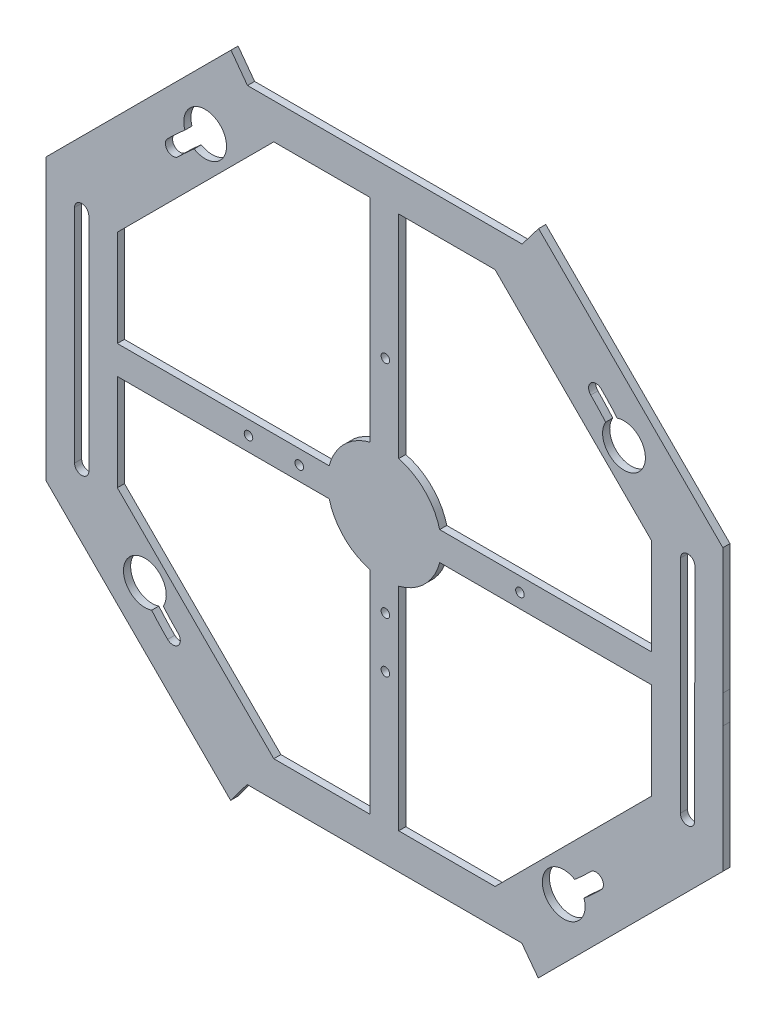
SolidWorks part; units mm, degrees
material "6061-T6 (SS)"
ref_plane "Front Plane" through (0, 0, 0) normal (0, 0, 1) x (1, 0, 0)
ref_plane "Top Plane" through (0, 0, 0) normal (0, 1, 0) x (1, 0, 0)
ref_plane "Right Plane" through (0, 0, 0) normal (1, 0, 0) x (0, 0, -1)
sketch "Sketch1" plane through (0, 0, 0) normal (0, 0, 1) x (1, 0, 0)
  line L0 (-150.6696, -62.417) -> (-62.404, -150.675)
  line L1 (-137.9698, -57.1559) -> (-57.1441, -137.9748)
  line L2 (-57.1441, -137.9748) -> (57.1559, -137.9698)
  line L3 (57.1559, -137.9698) -> (137.9748, -57.1441)
  line L4 (137.9748, -57.1441) -> (137.9698, 57.1559)
  line L5 (137.9698, 57.1559) -> (57.1441, 137.9748)
  line L6 (57.1441, 137.9748) -> (-57.1559, 137.9698)
  line L7 (-57.1559, 137.9698) -> (-137.9748, 57.1441)
  line L8 (-137.9748, 57.1441) -> (-137.9698, -57.1559)
  line L9 (-62.404, -150.675) -> (62.417, -150.6696)
  line L10 (62.417, -150.6696) -> (150.675, -62.404)
  line L11 (150.675, -62.404) -> (150.6696, 62.417)
  line L12 (150.6696, 62.417) -> (62.404, 150.675)
  line L13 (62.404, 150.675) -> (-62.417, 150.6696)
  line L14 (-62.417, 150.6696) -> (-150.675, 62.404)
  line L15 (-150.675, 62.404) -> (-150.6696, -62.417)
  circle A0 centre (0, 0) radius 137.9723 construction
  circle A1 centre (0, 0) radius 150.6723 construction
  dimension "D2" = 12.7
  dimension "D1" = 114.3
extrude "Boss-Extrude1" add sketch "Sketch1" along normal blind 3.175
sketch "Sketch2" plane through (0, 0, 3.175) normal (0, 0, 1) x (1, 0, 0)
  line L0 (57.1441, 137.9748) -> (-57.1559, 137.9698) construction
  line L1 (-57.1559, 137.9698) -> (-137.9748, 57.1441) construction
  line L2 (-104.3003, 90.8215) -> (-90.8305, 104.2924)
  line L3 (106.5368, 106.546) -> (97.5569, 97.5654) construction
  line L4 (-0.0059, 137.9723) -> (0.0059, -137.9723) construction
  line L5 (-57.1441, -137.9748) -> (57.1559, -137.9698) construction
  line L6 (-150.6723, -0.0065) -> (150.6723, 0.0065) construction
  line L7 (-150.675, 62.404) -> (-150.6696, -62.417) construction
  line L8 (150.675, -62.404) -> (150.6696, 62.417) construction
  line L9 (-106.546, 106.5368) -> (-97.5654, 97.5569) construction
  line L10 (-62.417, 150.6696) -> (-150.675, 62.404) construction
  line L11 (104.2924, 90.8305) -> (90.8215, 104.3003)
  line L12 (-106.5368, -106.546) -> (-97.5569, -97.5654) construction
  line L13 (106.546, -106.5368) -> (97.5654, -97.5569) construction
  line L14 (104.3003, -90.8215) -> (90.8305, -104.2924)
  line L15 (-104.2924, -90.8305) -> (-90.8215, -104.3003)
  line L16 (-97.5654, 97.5569) -> (-90.8299, 90.822) construction
  line L17 (97.5569, 97.5654) -> (90.822, 90.8299) construction
  line L18 (-97.5569, -97.5654) -> (-90.822, -90.8299) construction
  line L19 (97.5654, -97.5569) -> (90.8299, -90.822) construction
  arc A0 (-90.8305, 104.2924) -> (-104.3003, 90.8215) centre (-97.5654, 97.5569) cw
  arc A1 (90.8215, 104.3003) -> (104.2924, 90.8305) centre (97.5569, 97.5654) ccw
  arc A2 (90.8305, -104.2924) -> (104.3003, -90.8215) centre (97.5654, -97.5569) cw
  arc A3 (-90.8215, -104.3003) -> (-104.2924, -90.8305) centre (-97.5569, -97.5654) ccw
  circle A4 centre (-94.1976, 94.1895) radius 3.302
  circle A5 centre (94.1895, 94.1976) radius 3.302
  circle A6 centre (-94.1895, -94.1976) radius 3.302
  circle A7 centre (94.1976, -94.1895) radius 3.302
  dimension "D1" = 9.525
  dimension "D2" = 6.604
extrude "Boss-Extrude2" add sketch "Sketch2" against normal blind 3.175
sketch "Sketch4" plane through (0, 0, 3.175) normal (0, 0, 1) x (1, 0, 0)
  line L0 (-137.9748, 57.1441) -> (-137.9698, -57.1559) construction
  circle A0 centre (0, 0) radius 137.9723 construction
  circle A1 centre (0, 0) radius 25.4
  dimension "D1" = 50.8
sketch "Sketch5" plane through (0, 0, 3.175) normal (0, 0, 1) x (1, 0, 0)
  line L4 (-0.0065, 150.6723) -> (0.0065, -150.6723) construction
  line L5 (62.404, 150.675) -> (-62.417, 150.6696) construction
  line L6 (-62.404, -150.675) -> (62.417, -150.6696) construction
  line L7 (-150.6723, -0.0065) -> (150.6723, 0.0065) construction
  line L8 (-150.675, 62.404) -> (-150.6696, -62.417) construction
  line L9 (150.675, -62.404) -> (150.6696, 62.417) construction
  line L16 (137.9698, 57.1559) -> (104.2924, 90.8305) construction
  line L17 (137.9748, -57.1441) -> (137.9698, 57.1559) construction
  line L18 (104.3003, -90.8215) -> (137.9748, -57.1441) construction
  line L19 (137.9704, 44.4559) -> (137.9698, 57.1559)
  line L20 (137.9698, 57.1559) -> (128.9892, 66.1358)
  line L21 (128.9949, -66.1247) -> (137.9748, -57.1441)
  line L22 (137.9748, -57.1441) -> (137.9742, -44.4441)
  line L23 (-137.9698, -57.1559) -> (-137.9704, -44.4559)
  line L24 (-128.9892, -66.1358) -> (-137.9698, -57.1559)
  line L25 (-137.9742, 44.4441) -> (-137.9748, 57.1441)
  line L26 (-137.9748, 57.1441) -> (-128.9949, 66.1247)
  arc A4 (128.9892, 66.1358) -> (137.9704, 44.4559) centre (137.9698, 57.1559) ccw
  arc A5 (137.9742, -44.4441) -> (128.9949, -66.1247) centre (137.9748, -57.1441) ccw
  arc A6 (-137.9704, -44.4559) -> (-128.9892, -66.1358) centre (-137.9698, -57.1559) cw
  arc A7 (-128.9949, 66.1247) -> (-137.9742, 44.4441) centre (-137.9748, 57.1441) cw
  dimension "D2" = 12.7
  dimension "D3" = 12.7
extrude "Boss-Extrude3" add sketch "Sketch5" against normal blind 3.175
sketch "Sketch9" plane through (0, 0, 0) normal (0, 0, -1) x (-1, 0, 0)
  line L0 (-49.2541, 118.9244) -> (-118.9202, 49.2644)
  line L1 (-57.1441, 137.9748) -> (-137.9698, 57.1559)
  line L2 (-137.9698, 57.1559) -> (-137.9748, -57.1441)
  line L3 (-137.9748, -57.1441) -> (-57.1559, -137.9698)
  line L4 (-57.1559, -137.9698) -> (57.1441, -137.9748)
  line L5 (57.1441, -137.9748) -> (137.9698, -57.1559)
  line L6 (137.9698, -57.1559) -> (137.9748, 57.1441)
  line L7 (137.9748, 57.1441) -> (57.1559, 137.9698)
  line L8 (57.1559, 137.9698) -> (-57.1441, 137.9748)
  line L9 (-118.9202, 49.2644) -> (-118.9244, -49.2541)
  line L10 (-118.9244, -49.2541) -> (-49.2644, -118.9202)
  line L11 (-49.2644, -118.9202) -> (49.2541, -118.9244)
  line L12 (49.2541, -118.9244) -> (118.9202, -49.2644)
  line L13 (118.9202, -49.2644) -> (118.9244, 49.2541)
  line L14 (118.9244, 49.2541) -> (49.2644, 118.9202)
  line L15 (49.2644, 118.9202) -> (-49.2541, 118.9244)
  circle A0 centre (0, 0) radius 137.9723 construction
  dimension "D1" = 19.05
extrude "Boss-Extrude4" add sketch "Sketch9" against normal blind 3.175
sketch "Sketch10" plane through (0, 0, 0) normal (0, 0, 1) x (1, 0, 0)
  line L2 (-104.3003, 90.8215) -> (-90.8305, 104.2924) construction
  line L3 (106.5368, 106.546) -> (97.5569, 97.5654) construction
  line L4 (-0.0059, 137.9723) -> (0.0059, -137.9723) construction
  line L6 (-150.6723, -0.0065) -> (150.6723, 0.0065) construction
  line L9 (-106.546, 106.5368) -> (-97.5654, 97.5569) construction
  line L11 (104.2924, 90.8305) -> (90.8215, 104.3003) construction
  line L12 (-106.5368, -106.546) -> (-97.5569, -97.5654) construction
  line L13 (106.546, -106.5368) -> (97.5654, -97.5569) construction
  line L14 (104.3003, -90.8215) -> (90.8305, -104.2924) construction
  line L15 (-104.2924, -90.8305) -> (-90.8215, -104.3003) construction
  line L16 (-97.5654, 97.5569) -> (-90.8299, 90.822) construction
  line L17 (97.5569, 97.5654) -> (90.822, 90.8299) construction
  line L18 (-97.5569, -97.5654) -> (-90.822, -90.8299) construction
  line L19 (97.5654, -97.5569) -> (90.8299, -90.822) construction
  arc A0 (-90.8305, 104.2924) -> (-104.3003, 90.8215) centre (-97.5654, 97.5569) cw construction
  arc A1 (90.8215, 104.3003) -> (104.2924, 90.8305) centre (97.5569, 97.5654) ccw construction
  arc A2 (90.8305, -104.2924) -> (104.3003, -90.8215) centre (97.5654, -97.5569) cw construction
  arc A3 (-90.8215, -104.3003) -> (-104.2924, -90.8305) centre (-97.5569, -97.5654) ccw construction
  circle A4 centre (-94.1976, 94.1895) radius 3.302
  circle A5 centre (94.1895, 94.1976) radius 3.302
  circle A6 centre (-94.1895, -94.1976) radius 3.302
  circle A7 centre (94.1976, -94.1895) radius 3.302
  dimension "D1" = 9.525
  dimension "D2" = 6.604
extrude "Cut-Extrude2" cut sketch "Sketch10" along normal blind 3.175
sketch "Sketch11" plane through (0, 0, 0) normal (0, 0, -1) x (-1, 0, 0)
  line L1 (-94.1895, 97.4996) -> (-132.7919, 97.4996)
  line L2 (-94.1895, 97.4996) -> (-94.1895, 90.8956)
  line L3 (-94.1895, 90.8956) -> (-132.7919, 90.8956)
  line L4 (-132.7919, 97.4996) -> (-132.7919, 90.8956)
  line L5 (-94.1976, -90.8875) -> (-138.8409, -90.8875)
  line L6 (-94.1976, -90.8875) -> (-94.1976, -97.4915)
  line L7 (-94.1976, -97.4915) -> (-138.8409, -97.4915)
  line L8 (-138.8409, -90.8875) -> (-138.8409, -97.4915)
  line L9 (94.1976, 97.4915) -> (65.8814, 97.4915)
  line L10 (94.1976, 97.4915) -> (94.1976, 90.8875)
  line L11 (94.1976, 90.8875) -> (65.8814, 90.8875)
  line L12 (65.8814, 97.4915) -> (65.8814, 90.8875)
  line L13 (94.1895, -90.8956) -> (55.4466, -90.8956)
  line L14 (94.1895, -90.8956) -> (94.1895, -97.4996)
  line L15 (94.1895, -97.4996) -> (55.4466, -97.4996)
  line L16 (55.4466, -90.8956) -> (55.4466, -97.4996)
  circle A0 centre (-94.1895, 94.1976) radius 3.302 construction
  circle A1 centre (-94.1976, -94.1895) radius 3.302 construction
  circle A2 centre (94.1976, 94.1895) radius 3.302 construction
  circle A3 centre (94.1895, -94.1976) radius 3.302 construction
  dimension "D1" = 6.604
  dimension "D2" = 6.604
  dimension "D3" = 6.604
  dimension "D4" = 38.6024
extrude "Cut-Extrude3" [suppressed] cut sketch "Sketch11" against normal blind 3.175
sketch "Sketch12" plane through (0, 0, 0) normal (0, 0, -1) x (-1, 0, 0)
  line L0 (62.404, -150.675) -> (-62.417, -150.6696) construction
  line L1 (6.35, 150.672) -> (-6.35, 150.672)
  line L2 (6.35, 150.672) -> (6.35, 6.35)
  line L3 (6.35, -150.672) -> (-6.35, -150.672)
  line L4 (-6.35, 150.672) -> (-6.35, 6.35)
  line L7 (-150.675, -62.404) -> (-150.6696, 62.417) construction
  line L8 (150.6726, 6.35) -> (6.35, 6.35)
  line L9 (150.6726, 6.35) -> (150.6726, -6.35)
  line L10 (150.6726, -6.35) -> (6.35, -6.35)
  line L11 (-150.6726, 6.35) -> (-150.6726, -6.35)
  line L15 (6.35, -6.35) -> (6.35, -150.672)
  line L18 (-6.35, 6.35) -> (-150.6726, 6.35)
  line L20 (-6.35, -6.35) -> (-6.35, -150.672)
  line L21 (-6.35, -6.35) -> (-150.6726, -6.35)
  point P0 (0, 0)
  point P8 (0, 0)
  dimension "D1" = 12.7
  dimension "D2" = 12.7
extrude "Boss-Extrude6" add sketch "Sketch12" against normal blind 3.175
hole_wizard "#6 Clearance Hole1" positions "Sketch14" profile "Sketch13" hole size "#6" standard "Ansi Inch"
sketch "Sketch14" plane through (0, 0, 0) normal (0, 0, -1) x (-1, 0, 0)
  line L0 (0.0065, 150.6723) -> (-0.0065, -150.6723) construction
  line L1 (-62.404, 150.675) -> (62.417, 150.6696) construction
  line L2 (62.404, -150.675) -> (-62.417, -150.6696) construction
  line L4 (150.6726, 0) -> (-150.6726, 0) construction
  line L5 (150.6726, -6.35) -> (150.6726, 6.35) construction
  line L6 (-150.6726, 6.35) -> (-150.6726, -6.35) construction
  point P0 (-0.4188, 60.325)
  point P1 (-0.4188, -37.9222)
  point P3 (-0.4188, -60.5231)
  point P5 (37.9222, 0)
  point P7 (60.5231, 0)
  point P9 (-60.325, 0)
  dimension "D1" = 60.325
  dimension "D2" = 98.2472
  dimension "D3" = 22.6009
  dimension "D4" = 60.325
  dimension "D5" = 98.2472
  dimension "D6" = 22.6009
sketch "Sketch13" plane through (0.4188, 60.325, 0) normal (1, 0, 0) x (0, 1, 0)
  line L0 (0, 0) -> (0, 26.5408)
  line L1 (0, 26.5408) -> (1.8986, 25.4)
  line L2 (1.8986, 25.4) -> (1.8986, 0)
  line L5 (1.8986, 0) -> (0, 0)
  line L10 (0, 26.5408) -> (-1.8986, 25.4) construction
  line L11 (0, -6.35) -> (0, 107.95) construction
  dimension "Hole Dia." = 3.7973
  dimension "Hole Depth" = 25.4
  dimension "Drill Angle" = 118
sketch "Sketch15" plane through (0, 0, 0) normal (0, 0, -1) x (-1, 0, 0)
  line L0 (0.0065, 150.6723) -> (-0.0065, -150.6723) construction
  line L1 (73.025, 117.475) -> (-73.025, 117.475) construction
  line L2 (73.025, 117.475) -> (73.025, -117.475) construction
  line L3 (73.025, -117.475) -> (-73.025, -117.475) construction
  line L4 (-73.025, 117.475) -> (-73.025, -117.475) construction
  line L5 (73.025, 117.475) -> (-73.025, -117.475) construction
  line L6 (73.025, -117.475) -> (-73.025, 117.475) construction
  line L7 (-73.025, 120.015) -> (-111.125, 120.015)
  line L8 (-62.404, 150.675) -> (62.417, 150.6696) construction
  line L9 (-73.025, 114.935) -> (-111.125, 114.935)
  line L10 (-111.125, 120.015) -> (-111.125, 114.935)
  line L11 (62.404, -150.675) -> (-62.417, -150.6696) construction
  line L12 (-150.6726, 0) -> (150.6726, 0) construction
  line L13 (-150.6726, 6.35) -> (-150.6726, -6.35) construction
  line L14 (150.6726, -6.35) -> (150.6726, 6.35) construction
  line L15 (73.025, 114.935) -> (47.625, 114.935)
  line L16 (73.025, 120.015) -> (47.625, 120.015)
  line L17 (47.625, 120.015) -> (47.625, 114.935)
  line L18 (-73.025, -120.015) -> (-111.125, -120.015)
  line L19 (-73.025, -114.935) -> (-111.125, -114.935)
  line L20 (-111.125, -114.935) -> (-111.125, -120.015)
  line L21 (73.025, -114.935) -> (47.625, -114.935)
  line L22 (73.025, -120.015) -> (47.625, -120.015)
  line L23 (47.625, -114.935) -> (47.625, -120.015)
  arc A0 (-73.025, 120.015) -> (-73.025, 114.935) centre (-73.025, 117.475) cw
  arc A1 (73.025, 120.015) -> (73.025, 114.935) centre (73.025, 117.475) cw
  arc A2 (-73.025, -114.935) -> (-73.025, -120.015) centre (-73.025, -117.475) cw
  arc A3 (73.025, -114.935) -> (73.025, -120.015) centre (73.025, -117.475) cw
  point P0 (0, 0)
  dimension "D5" = 2.54
  dimension "D1" = 146.05
  dimension "D2" = 234.95
  dimension "D3" = 2.54
  dimension "D4" = 2.54
  dimension "D6" = 38.1
  dimension "D7" = 25.4
  dimension "D8" = 38.1
extrude "Cut-Extrude4" [suppressed] cut sketch "Sketch15" against normal blind 3.175
sketch "Sketch16" plane through (0, 0, 0) normal (0, 0, -1) x (-1, 0, 0)
  line L0 (-62.404, 150.675) -> (-49.2541, 118.9244) construction
  line L1 (-80.3653, 132.7153) -> (-56.5435, 136.5246)
  line L2 (-150.6696, 62.417) -> (-62.404, 150.675) construction
  line L3 (-56.5435, 136.5246) -> (-24.304, 150.6734)
  line L4 (-62.404, 150.675) -> (62.417, 150.6696) construction
  line L5 (-80.3653, 132.7153) -> (-62.404, 150.675)
  line L6 (-62.404, 150.675) -> (-24.304, 150.6734)
  line L7 (0.0065, 150.6723) -> (-0.0065, -150.6723) construction
  line L8 (62.404, -150.675) -> (-62.417, -150.6696) construction
  line L9 (-150.6726, 0) -> (150.6726, 0) construction
  line L10 (-150.6726, 6.35) -> (-150.6726, -6.35) construction
  line L11 (150.6726, -6.35) -> (150.6726, 6.35) construction
  line L12 (80.3767, 132.7083) -> (62.417, 150.6696)
  line L13 (62.417, 150.6696) -> (24.317, 150.6713)
  line L14 (56.5552, 136.5198) -> (24.317, 150.6713)
  line L15 (80.3767, 132.7083) -> (56.5552, 136.5198)
  line L16 (49.2541, -118.9244) -> (62.404, -150.675) construction
  line L17 (62.404, -150.675) -> (80.3653, -132.7153)
  line L18 (150.6696, -62.417) -> (62.404, -150.675) construction
  line L19 (80.3653, -132.7153) -> (56.5435, -136.5246)
  line L20 (56.5435, -136.5246) -> (24.304, -150.6734)
  line L21 (24.304, -150.6734) -> (62.404, -150.675)
  line L22 (-62.417, -150.6696) -> (-80.3767, -132.7083)
  line L23 (-80.3767, -132.7083) -> (-56.5552, -136.5198)
  line L24 (-56.5552, -136.5198) -> (-24.317, -150.6713)
  line L25 (-24.317, -150.6713) -> (-62.417, -150.6696)
  dimension "D1" = 25.4
  dimension "D2" = 38.1
  dimension "D3" = 19.05
  dimension "D4" = 38.1
  dimension "D5" = 25.4
  dimension "D6" = 19.05
extrude "Cut-Extrude5" [suppressed] cut sketch "Sketch16" against normal blind 4.7625
sketch "Sketch17" plane through (0, 0, 0) normal (0, 0, -1) x (-1, 0, 0)
  line L0 (-49.2541, 118.9244) -> (-73.3836, 150.6755) construction
  line L1 (-49.2644, -118.9202) -> (-73.0316, -150.6692) construction
  line L2 (72.6664, 150.6692) -> (49.2644, 118.9202) construction
  line L3 (-73.3836, 150.6755) -> (-61.3189, 134.7999)
  line L4 (-61.3189, 134.7999) -> (60.9654, 134.7947)
  line L5 (60.9654, 134.7947) -> (72.6664, 150.6692)
  line L6 (72.6664, 150.6692) -> (-73.3836, 150.6755)
  line L7 (-150.6726, 0) -> (150.6726, 0) construction
  line L8 (-150.6726, 6.35) -> (-150.6726, -6.35) construction
  line L9 (150.6726, -6.35) -> (150.6726, 6.35) construction
  line L10 (49.2541, -118.9244) -> (73.0184, -150.6755) construction
  line L11 (-61.148, -134.7947) -> (61.1362, -134.7999)
  line L12 (61.1362, -134.7999) -> (73.0184, -150.6755)
  line L13 (73.0184, -150.6755) -> (-73.0316, -150.6692)
  line L14 (-62.404, 150.675) -> (62.417, 150.6696) construction
  line L15 (-73.0316, -150.6692) -> (-61.148, -134.7947)
  line L16 (62.404, -150.675) -> (-62.417, -150.6696) construction
  dimension "D1" = 146.05
  dimension "D2" = 146.05
extrude "Cut-Extrude8" cut sketch "Sketch17" against normal blind 4.7625
extrude "Boss-Extrude7" add sketch "Sketch4" against normal blind 3.175
sketch "Sketch18" plane through (0, 0, 3.175) normal (0, 0, 1) x (1, 0, 0)
  line L0 (0, 0) -> (94.1895, 94.1976) construction
  arc A0 (94.1895, 94.1976) -> (106.6531, 79.8121) centre (0, 0) cw construction
  arc A1 (109.2968, 81.7905) -> (96.5243, 96.5326) centre (0, 0) ccw
  arc A2 (104.0094, 77.8337) -> (91.8547, 91.8626) centre (0, 0) ccw
  arc A3 (104.0094, 77.8337) -> (109.2968, 81.7905) centre (106.6531, 79.8121) ccw
  arc A4 (96.5243, 96.5326) -> (91.8547, 91.8626) centre (94.1895, 94.1976) ccw
  arc A5 (94.1976, -94.1895) -> (79.8121, -106.6531) centre (0, 0) cw construction
  arc A6 (81.7905, -109.2968) -> (96.5326, -96.5243) centre (0, 0) ccw
  arc A7 (77.8337, -104.0094) -> (91.8626, -91.8547) centre (0, 0) ccw
  arc A8 (77.8337, -104.0094) -> (81.7905, -109.2968) centre (79.8121, -106.6531) ccw
  arc A9 (96.5326, -96.5243) -> (91.8626, -91.8547) centre (94.1976, -94.1895) ccw
  arc A10 (-94.1895, -94.1976) -> (-106.6531, -79.8121) centre (0, 0) cw construction
  arc A11 (-109.2968, -81.7905) -> (-96.5243, -96.5326) centre (0, 0) ccw
  arc A12 (-104.0094, -77.8337) -> (-91.8547, -91.8626) centre (0, 0) ccw
  arc A13 (-104.0094, -77.8337) -> (-109.2968, -81.7905) centre (-106.6531, -79.8121) ccw
  arc A14 (-96.5243, -96.5326) -> (-91.8547, -91.8626) centre (-94.1895, -94.1976) ccw
  arc A15 (-94.1976, 94.1895) -> (-79.8121, 106.6531) centre (0, 0) cw construction
  arc A16 (-81.7905, 109.2968) -> (-96.5326, 96.5243) centre (0, 0) ccw
  arc A17 (-77.8337, 104.0094) -> (-91.8626, 91.8547) centre (0, 0) ccw
  arc A18 (-77.8337, 104.0094) -> (-81.7905, 109.2968) centre (-79.8121, 106.6531) ccw
  arc A19 (-96.5326, 96.5243) -> (-91.8626, 91.8547) centre (-94.1976, 94.1895) ccw
  point P3 (100.6786, 87.2277)
  point P11 (87.2277, -100.6786)
  point P16 (-100.6786, -87.2277)
  point P27 (-87.2277, 100.6786)
extrude "Cut-Extrude9" cut sketch "Sketch18" against normal blind 3.175
sketch "Sketch19" plane through (0, 0, 3.175) normal (0, 0, 1) x (1, 0, 0)
  circle A0 centre (-79.8121, 106.6531) radius 9.525
  circle A1 centre (106.6531, 79.8121) radius 9.525
  circle A2 centre (79.8121, -106.6531) radius 9.525
  circle A3 centre (-106.6531, -79.8121) radius 9.525
  dimension "D1" = 19.05
  dimension "D2" = 19.05
  dimension "D3" = 19.05
  dimension "D4" = 19.05
extrude "Cut-Extrude10" cut sketch "Sketch19" against normal blind 3.175
sketch "Sketch20" [suppressed] plane through (0, 0, 3.175) normal (0, 0, 1) x (1, 0, 0)
  line L0 (0, 0) -> (84.0871, 84.0944) construction
  line L1 (49.2541, 118.9244) -> (118.9202, 49.2644) construction
  line L2 (53.8792, 53.8839) -> (6.35, 53.8839) construction
  line L3 (6.35, 118.9226) -> (6.35, 24.5934) construction
  line L4 (53.8792, 53.8839) -> (53.8792, 6.35) construction
  line L5 (24.5934, 6.35) -> (118.922, 6.35) construction
  line L6 (57.0542, 15.9164) -> (57.0542, 6.35)
  line L7 (57.0542, 57.0589) -> (57.0539, 57.0589)
  line L8 (50.7042, 50.7089) -> (50.7042, 50.7086)
  line L9 (15.9117, 50.7089) -> (6.35, 50.7089)
  line L10 (57.0542, 6.35) -> (50.7042, 6.35)
  line L11 (6.35, 57.0589) -> (6.35, 50.7089)
  line L12 (15.9117, 57.0589) -> (6.35, 57.0589)
  line L13 (50.7042, 15.9164) -> (50.7042, 6.35)
  line L14 (57.0542, 57.0589) -> (6.35, 57.0589) construction
  line L15 (50.7042, 50.7089) -> (6.35, 50.7089) construction
  line L16 (84.0871, 84.0944) -> (72.5466, 72.5528) construction
  line L17 (50.7042, 50.7089) -> (50.7042, 6.35) construction
  line L18 (57.0542, 57.0589) -> (57.0542, 6.35) construction
  line L19 (81.842, 86.3394) -> (78.48, 82.977)
  line L20 (86.3323, 81.8494) -> (82.9703, 78.4871)
  line L21 (81.842, 86.3394) -> (86.3323, 81.8494)
  line L24 (81.842, 86.3394) -> (70.3014, 74.7978) construction
  line L25 (86.3323, 81.8494) -> (74.7917, 70.3079) construction
  arc A0 (57.0542, 15.9164) -> (82.9703, 78.4871) centre (53.8792, 53.8839) ccw
  arc A1 (15.9117, 50.7089) -> (50.7042, 15.9164) centre (53.8792, 53.8839) ccw
  arc A2 (78.48, 82.977) -> (15.9117, 57.0589) centre (53.8792, 53.8839) ccw
  dimension "D1" = 76.2
  dimension "D2" = 76.2
  dimension "D3" = 3.175
  dimension "D4" = 3.175
  dimension "D5" = 3.175
  dimension "D6" = 3.175
extrude "Boss-Extrude8" [suppressed] add sketch "Sketch20" against normal blind 3.175
sketch "Sketch21" [suppressed] plane through (0, 0, 3.175) normal (0, 0, 1) x (1, 0, 0)
  line L0 (53.9634, 194.1008) -> (53.9634, 60.7508) construction
  line L1 (63.8779, 72.3816) -> (65.1741, 72.7765)
  line L2 (66.9032, 48.8719) -> (67.3108, 47.5021)
  line L3 (63.5319, 63.5782) -> (63.4209, 61.5899)
  line L4 (51.4565, 46.7364) -> (51.3703, 45.4764)
  spline S0 degree 3 poles (48.9871, 84.173) (49.4073, 84.4944) (50.2592, 85.1485) (50.6915, 85.4819) knots 0 0 0 0 1 1 1 1
  spline S1 degree 3 poles (50.6915, 85.4819) (49.7407, 83.2717) (48.6416, 81.1356) (47.8265, 78.876) knots 1 1 1 1 2 2 2 2
  spline S2 degree 3 poles (47.8265, 78.876) (51.7405, 78.8266) (55.6677, 78.8145) (59.5817, 78.9381) knots 2 2 2 2 3 3 3 3
  spline S3 degree 3 poles (59.5817, 78.9381) (58.7907, 81) (57.7296, 82.951) (57.0001, 85.0376) knots 3 3 3 3 4 4 4 4
  spline S4 degree 3 poles (57.0001, 85.0376) (58.0998, 84.914) (58.9149, 84.0494) (59.4696, 82.4445) knots 4 4 4 4 5 5 5 5
  spline S5 degree 3 poles (59.4696, 82.4445) (60.4089, 80.827) (61.4205, 79.2468) (62.5323, 77.7402) knots 5 5 5 5 6 6 6 6
  spline S6 degree 3 poles (62.5323, 77.7402) (56.6553, 77.4068) (50.753, 77.2464) (44.876, 77.6045) knots 6 6 6 6 7 7 7 7
  spline S7 degree 3 poles (44.876, 77.6045) (46.2958, 79.7526) (47.6414, 81.9628) (48.9871, 84.173) knots 7 7 7 7 8 8 8 8
  spline S8 degree 3 poles (55.6304, 76.172) (58.2228, 76.0117) (60.8164, 76.1105) (63.3968, 76.1847) knots 0 0 0 0 1 1 1 1
  spline S9 degree 3 poles (63.3968, 76.1847) (63.3474, 75.5179) (63.2485, 74.1964) (63.1991, 73.5422) knots 1 1 1 1 2 2 2 2
  spline S10 degree 3 poles (63.1991, 73.5422) (60.5813, 73.7026) (56.4201, 72.5915) (55.6304, 76.172) knots 2 2 2 2 3 3 3 3
  spline S11 degree 3 poles (44.5673, 74.1475) (47.0367, 74.6781) (49.5677, 74.5298) (52.0739, 74.5298) knots 0 0 0 0 1 1 1 1
  spline S12 degree 3 poles (52.0739, 74.5298) (54.383, 73.8135) (55.6677, 71.6286) (57.5198, 70.2329) knots 1 1 1 1 2 2 2 2
  spline S13 degree 3 poles (57.5198, 70.2329) (59.4828, 70.1714) (61.4459, 70.3813) (63.3848, 70.0973) knots 2 2 2 2 3 3 3 3
  spline S14 degree 3 poles (63.3848, 70.0973) (63.4089, 69.2701) (63.4463, 67.6158) (63.4704, 66.776) knots 3 3 3 3 4 4 4 4
  spline S15 degree 3 poles (63.4704, 66.776) (61.8414, 66.5909) (60.2726, 65.739) (58.6062, 65.9241) knots 4 4 4 4 5 5 5 5
  spline S16 degree 3 poles (58.6062, 65.9241) (56.173, 67.8871) (54.0622, 70.2082) (51.679, 72.246) knots 5 5 5 5 6 6 6 6
  spline S17 degree 3 poles (51.679, 72.246) (49.4567, 73.1226) (45.1599, 71.0113) (44.5673, 74.1475) knots 6 6 6 6 7 7 7 7
  spline S18 degree 3 poles (66.3848, 74.5298) (69.8791, 72.5788) (73.1878, 70.2824) (76.447, 67.9739) knots 0 0 0 0 1 1 1 1
  spline S19 degree 3 poles (76.447, 67.9739) (79.2746, 63.2569) (81.4607, 58.1576) (83.9181, 53.2428) knots 1 1 1 1 2 2 2 2
  spline S20 degree 3 poles (83.9181, 53.2428) (84.0037, 50.2055) (83.3128, 47.2175) (83.1403, 44.1922) knots 2 2 2 2 3 3 3 3
  spline S21 degree 3 poles (83.1403, 44.1922) (82.5712, 41.6251) (82.3867, 38.9941) (81.9792, 36.4017) knots 3 3 3 3 4 4 4 4
  spline S22 degree 3 poles (81.9792, 36.4017) (80.6214, 37.7099) (79.3493, 39.1062) (77.9784, 40.4145) knots 4 4 4 4 5 5 5 5
  spline S23 degree 3 poles (77.9784, 40.4145) (76.5712, 42.0315) (75.0158, 43.5266) (73.4229, 44.9712) knots 5 5 5 5 6 6 6 6
  spline S24 degree 3 poles (73.4229, 44.9712) (72.0399, 46.353) (70.6195, 47.6998) (69.1508, 49.0081) knots 6 6 6 6 7 7 7 7
  spline S25 degree 3 poles (69.1508, 49.0081) (68.9651, 49.23) (68.5829, 49.6749) (68.3972, 49.8968) knots 7 7 7 7 8 8 8 8
  spline S26 degree 3 poles (68.3972, 49.8968) (67.9282, 50.4285) (66.9768, 51.4896) (66.5077, 52.0214) knots 8 8 8 8 9 9 9 9
  spline S27 degree 3 poles (66.5077, 52.0214) (64.3229, 52.0334) (62.1368, 51.9092) (59.9519, 51.9587) knots 9 9 9 9 10 10 10 10
  spline S28 degree 3 poles (59.9519, 51.9587) (57.6549, 53.1198) (56.3092, 55.6882) (53.9634, 56.689) knots 10 10 10 10 11 11 11 11
  spline S29 degree 3 poles (53.9634, 56.689) (50.6667, 56.6636) (47.3695, 56.5768) (44.0856, 56.6636) knots 11 11 11 11 12 12 12 12
  spline S30 degree 3 poles (44.0856, 56.6636) (44.0976, 58.3306) (44.5052, 59.8614) (45.3203, 61.2939) knots 12 12 12 12 13 13 13 13
  spline S31 degree 3 poles (45.3203, 61.2939) (47.1103, 61.3433) (48.9009, 61.368) (50.6915, 61.3554) knots 13 13 13 13 14 14 14 14
  spline S32 degree 3 poles (50.6915, 61.3554) (52.7654, 60.7754) (53.5926, 57.5029) (55.9764, 58.0587) knots 14 14 14 14 15 15 15 15
  spline S34 degree 3 poles (56.7047, 57.3799) (57.7043, 54.1821) (61.3964, 54.3425) (64.1131, 53.8735) knots 16 16 16 16 17 17 17 17
  spline S35 degree 3 poles (64.1131, 53.8735) (63.8044, 60.0465) (64.224, 66.2201) (63.8779, 72.3816) knots 17 17 17 17 18 18 18 18
  spline S36 degree 3 poles (65.1741, 72.7765) (67.3482, 68.2452) (70.6315, 64.3312) (73.7063, 60.3925) knots 19 19 19 19 20 20 20 20
  spline S37 degree 3 poles (73.7063, 60.3925) (71.1994, 65.0722) (68.8542, 69.826) (66.3848, 74.5298) knots 20 20 20 20 21 21 21 21
  spline S38 degree 3 poles (36.7882, 71.8879) (37.8251, 72.5667) (39.8997, 73.9251) (40.9367, 74.5919) knots 0 0 0 0 1 1 1 1
  spline S39 degree 3 poles (40.9367, 74.5919) (39.122, 70.1467) (36.5042, 66.0844) (34.6274, 61.652) knots 1 1 1 1 2 2 2 2
  spline S40 degree 3 poles (34.6274, 61.652) (38.2454, 65.0969) (40.0727, 69.9984) (43.7148, 73.3692) knots 2 2 2 2 3 3 3 3
  spline S41 degree 3 poles (43.7148, 73.3692) (43.0239, 66.8996) (44.876, 60.1827) (42.7767, 53.8976) knots 3 3 3 3 4 4 4 4
  spline S42 degree 3 poles (42.7767, 53.8976) (46.086, 54.8489) (49.555, 54.3666) (52.9505, 54.3787) knots 4 4 4 4 5 5 5 5
  spline S43 degree 3 poles (52.9505, 54.3787) (54.9262, 52.9595) (56.4949, 51.0459) (58.3217, 49.4398) knots 5 5 5 5 6 6 6 6
  spline S44 degree 3 poles (58.3217, 49.4398) (61.1746, 49.1444) (64.0142, 48.4776) (66.9032, 48.8719) knots 6 6 6 6 7 7 7 7
  spline S45 degree 3 poles (67.3108, 47.5021) (64.3349, 45.0447) (59.6553, 46.3663) (56.0005, 46.4651) knots 8 8 8 8 9 9 9 9
  spline S46 degree 3 poles (56.0005, 46.4651) (54.1979, 48.3908) (52.3084, 50.2549) (50.3086, 51.984) knots 9 9 9 9 10 10 10 10
  spline S47 degree 3 poles (50.3086, 51.984) (47.6541, 52.9715) (44.6041, 51.527) (42.0852, 53.1693) knots 10 10 10 10 11 11 11 11
  spline S48 degree 3 poles (42.0852, 53.1693) (40.7148, 51.861) (39.4306, 50.4647) (38.1585, 49.0696) knots 11 11 11 11 12 12 12 12
  spline S49 degree 3 poles (38.1585, 49.0696) (37.8499, 48.7368) (37.2325, 48.0821) (36.9238, 47.7493) knots 12 12 12 12 13 13 13 13
  spline S50 degree 3 poles (36.9238, 47.7493) (33.0346, 44.1066) (29.2195, 40.3771) (25.6883, 36.4017) knots 13 13 13 13 14 14 14 14
  spline S51 degree 3 poles (25.6883, 36.4017) (24.3421, 41.5624) (24.4162, 47.0692) (23.3419, 52.3168) knots 14 14 14 14 15 15 15 15
  spline S52 degree 3 poles (23.3419, 52.3168) (25.2681, 57.5403) (28.1945, 62.405) (30.5778, 67.4548) knots 15 15 15 15 16 16 16 16
  spline S53 degree 3 poles (30.5778, 67.4548) (32.3183, 69.3069) (34.7757, 70.3445) (36.7882, 71.8879) knots 16 16 16 16 17 17 17 17
  spline S54 degree 3 poles (44.1845, 68.0601) (43.6286, 71.4062) (48.506, 71.2331) (50.7777, 71.0728) knots 0 0 0 0 1 1 1 1
  spline S55 degree 3 poles (50.7777, 71.0728) (53.5311, 69.1833) (55.6545, 66.5288) (58.2602, 64.4422) knots 1 1 1 1 2 2 2 2
  spline S56 degree 3 poles (58.2602, 64.4422) (60.0375, 64.2818) (61.7919, 63.9357) (63.5319, 63.5782) knots 2 2 2 2 3 3 3 3
  spline S57 degree 3 poles (63.4209, 61.5899) (61.7292, 61.368) (60.0375, 61.3801) (58.3711, 61.6393) knots 4 4 4 4 5 5 5 5
  spline S58 degree 3 poles (58.3711, 61.6393) (56.0874, 63.6892) (53.9507, 65.9114) (51.5681, 67.8503) knots 5 5 5 5 6 6 6 6
  spline S59 degree 3 poles (51.5681, 67.8503) (49.1107, 67.998) (46.6292, 67.6773) (44.1845, 68.0601) knots 6 6 6 6 7 7 7 7
  spline S60 degree 3 poles (43.962, 65.7758) (46.1842, 66.0724) (48.4439, 66.0597) (50.6788, 65.9982) knots 0 0 0 0 1 1 1 1
  spline S61 degree 3 poles (50.6788, 65.9982) (53.346, 64.0967) (55.5194, 61.5778) (58.0998, 59.5774) knots 1 1 1 1 2 2 2 2
  spline S62 degree 3 poles (58.0998, 59.5774) (59.7421, 58.7623) (61.7425, 59.8493) (63.4704, 59.0957) knots 2 2 2 2 3 3 3 3
  spline S63 degree 3 poles (63.4704, 59.0957) (64.359, 54.861) (58.816, 56.7746) (56.7047, 57.3799) knots 3 3 3 3 4 4 4 4
  spline S65 degree 3 poles (55.9764, 58.0587) (55.9137, 60.4293) (52.6913, 60.9725) (51.4318, 62.7384) knots 5 5 5 5 6 6 6 6
  spline S66 degree 3 poles (51.4318, 62.7384) (49.4441, 62.8246) (47.4437, 62.7631) (45.456, 62.8493) knots 6 6 6 6 7 7 7 7
  spline S67 degree 3 poles (45.456, 62.8493) (45.0858, 63.5782) (44.3322, 65.0475) (43.962, 65.7758) knots 7 7 7 7 8 8 8 8
  spline S68 degree 3 poles (40.505, 48.65) (44.135, 47.7119) (48.506, 49.6749) (51.4565, 46.7364) knots 0 0 0 0 1 1 1 1
  spline S69 degree 3 poles (51.3703, 45.4764) (48.1973, 45.6995) (45.0116, 45.5753) (41.8259, 45.6247) knots 2 2 2 2 3 3 3 3
  spline S70 degree 3 poles (41.8259, 45.6247) (41.4925, 46.3783) (40.8257, 47.8964) (40.505, 48.65) knots 3 3 3 3 4 4 4 4
  spline S71 degree 3 poles (42.9371, 43.7364) (45.8882, 44.9832) (49.4441, 43.81) (52.6171, 44.279) knots 0 0 0 0 1 1 1 1
  spline S72 degree 3 poles (52.6171, 44.279) (56.7783, 44.2417) (60.9394, 44.4032) (65.0885, 44.0692) knots 1 1 1 1 2 2 2 2
  spline S73 degree 3 poles (65.0885, 44.0692) (64.7172, 43.6002) (63.9889, 42.6621) (63.6187, 42.193) knots 2 2 2 2 3 3 3 3
  spline S74 degree 3 poles (63.6187, 42.193) (57.1617, 42.3655) (50.6788, 42.2425) (44.2092, 42.2786) knots 3 3 3 3 4 4 4 4
  spline S75 degree 3 poles (44.2092, 42.2786) (43.9005, 42.6368) (43.2584, 43.3651) (42.9371, 43.7364) knots 4 4 4 4 5 5 5 5
  spline S76 degree 3 poles (51.6911, 37.8715) (52.9999, 38.0813) (54.3709, 38.3032) (55.6424, 37.7594) knots 0 0 0 0 1 1 1 1
  spline S77 degree 3 poles (55.6424, 37.7594) (54.9141, 35.9326) (54.6296, 33.9816) (54.4945, 32.0307) knots 1 1 1 1 2 2 2 2
  spline S78 degree 3 poles (54.4945, 32.0307) (53.3707, 33.8828) (52.5188, 35.8832) (51.6911, 37.8715) knots 2 2 2 2 3 3 3 3
extrude "Cut-Extrude11" [suppressed] cut sketch "Sketch21" against normal blind 3.175
sketch "Sketch22" plane through (0, 0, 3.175) normal (0, 0, 1) x (1, 0, 0)
  line L0 (-150.6726, 0) -> (-118.9235, 0) construction
  line L1 (-150.6726, -6.35) -> (-150.6726, 6.35) construction
  line L2 (-118.9244, 49.2541) -> (-150.6744, 49.2541) construction
  line L3 (-150.675, 62.404) -> (-150.6726, 6.35) construction
  line L4 (-118.9202, -49.2644) -> (-150.6702, -49.2644) construction
  line L5 (-150.672, -6.35) -> (-150.6696, -62.417) construction
  line L6 (-134.7994, 49.2541) -> (-134.7952, -49.2644) construction
  line L7 (-137.9744, 49.254) -> (-137.9702, -49.2645)
  line L8 (-131.6244, 49.2542) -> (-131.6202, -49.2642)
  line L9 (0.1768, 134.7973) -> (0.0059, -134.7973) construction
  line L10 (-60.9654, 134.7947) -> (61.3189, 134.7999) construction
  line L11 (61.148, -134.7947) -> (-61.1362, -134.7999) construction
  line L12 (135.0444, 49.0831) -> (134.9152, -49.4353) construction
  line L13 (119.0403, -49.4152) -> (150.7902, -49.4554) construction
  line L14 (119.1694, 49.1032) -> (150.9194, 49.0629) construction
  line L15 (150.8551, -0.1911) -> (119.106, -0.1509) construction
  line L16 (131.8694, 49.0872) -> (131.7402, -49.4312)
  line L17 (138.2194, 49.0789) -> (138.0902, -49.4395)
  arc A0 (-137.9744, 49.254) -> (-131.6244, 49.2542) centre (-134.7994, 49.2541) cw
  arc A1 (-137.9702, -49.2645) -> (-131.6202, -49.2642) centre (-134.7952, -49.2644) ccw
  arc A2 (138.0902, -49.4395) -> (131.7402, -49.4312) centre (134.9152, -49.4353) cw
  arc A3 (138.2194, 49.0789) -> (131.8694, 49.0872) centre (135.0444, 49.0831) ccw
  dimension "D1" = 3.175
  dimension "D2" = 3.175
extrude "Cut-Extrude12" cut sketch "Sketch22" against normal through all
